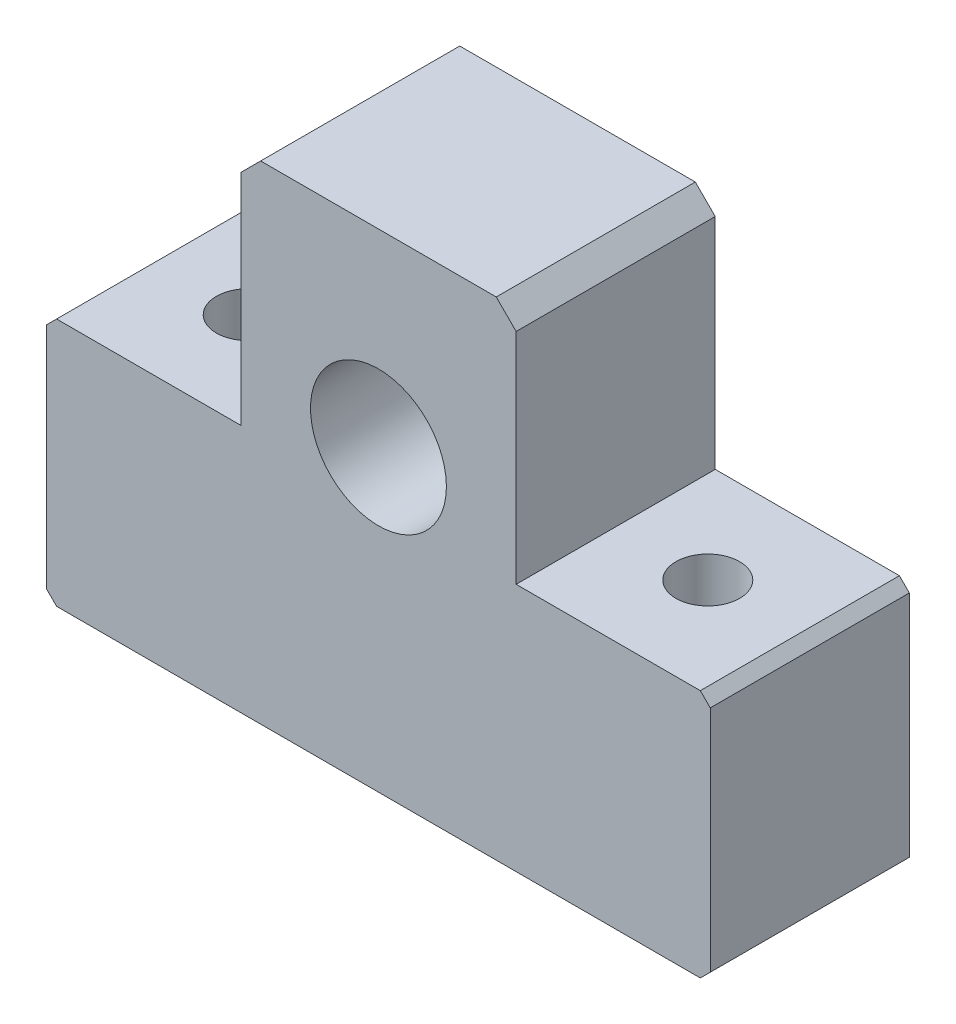
SolidWorks part; units mm, degrees
ref_plane "Front Plane" through (0, 0, 0) normal (0, 0, 1) x (1, 0, 0)
ref_plane "Top Plane" through (0, 0, 0) normal (0, 1, 0) x (1, 0, 0)
ref_plane "Right Plane" through (0, 0, 0) normal (1, 0, 0) x (0, 0, -1)
sketch "Sketch6" plane through (0, 0, 0) normal (0, 0, 1) x (1, 0, 0)
  line L0 (-250, -3.75) -> (-242.5, 3.75)
  line L1 (-242.5, 3.75) -> (-103.75, 3.75)
  line L2 (-103.75, 3.75) -> (-103.75, 168.75)
  line L3 (-103.75, 168.75) -> (-88.75, 183.75)
  line L4 (-88.75, 183.75) -> (88.75, 183.75)
  line L5 (242.5, -183.75) -> (-242.5, -183.75)
  line L6 (-242.5, -183.75) -> (-250, -176.25)
  line L7 (-250, -176.25) -> (-250, -3.75)
  line L10 (250, -176.25) -> (250, -3.75)
  line L11 (242.5, -183.75) -> (250, -176.25)
  line L12 (103.75, 168.75) -> (88.75, 183.75)
  line L13 (103.75, 3.75) -> (103.75, 168.75)
  line L14 (242.5, 3.75) -> (103.75, 3.75)
  line L15 (250, -3.75) -> (242.5, 3.75)
  circle A0 centre (0, 41.25) radius 51.2
extrude "Boss-Extrude4" add sketch "Sketch6" along normal blind 150
sketch "Sketch7" plane through (0, 3.75, 0) normal (0, 1, 0) x (1, 0, 0)
  circle A0 centre (-173.125, -75) radius 24
  dimension "D1" = 48
extrude "Cut-Extrude1" cut sketch "Sketch7" against normal through all contours A0
mirror "Mirror1" about plane through (0, 0, 0) normal (1, 0, 0) of "Cut-Extrude1"
